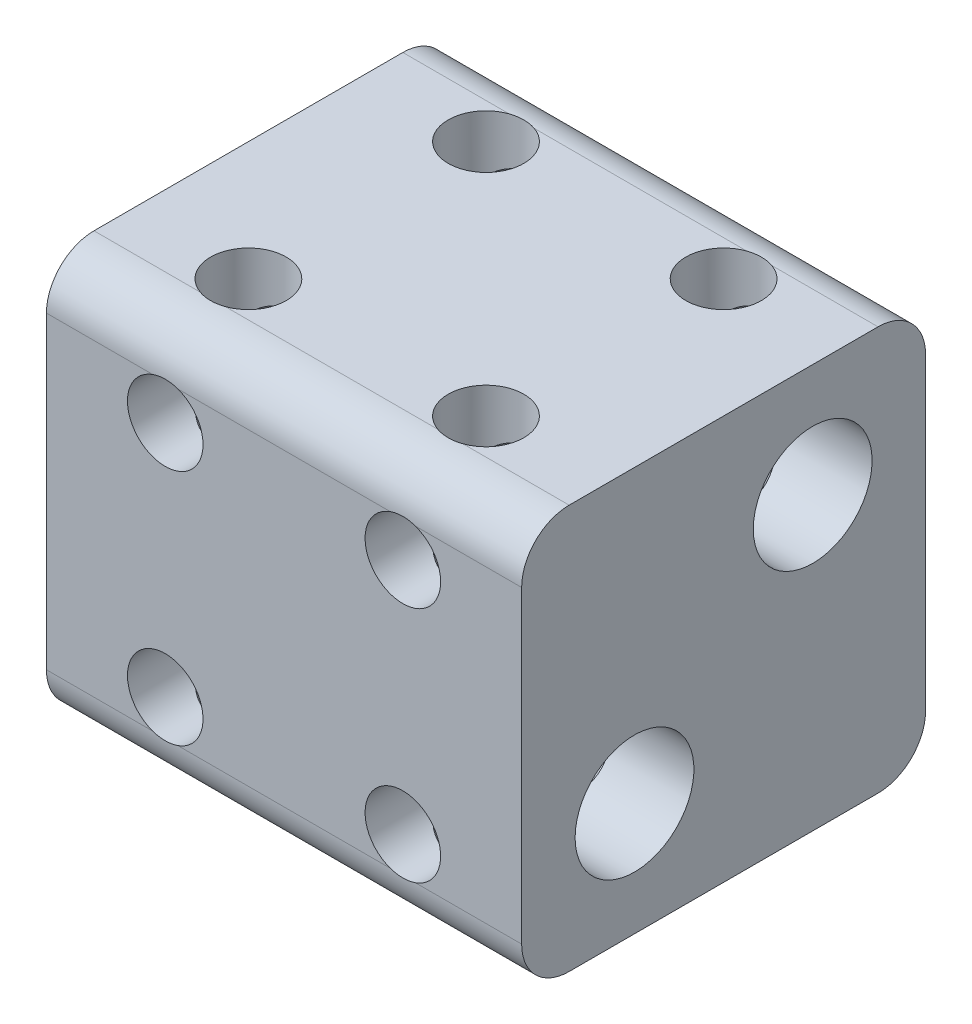
SolidWorks part; units mm, degrees
material "PET"
ref_plane "Front" through (0, 0, 0) normal (0, 0, 1) x (1, 0, 0)
ref_plane "Top" through (0, 0, 0) normal (0, 1, 0) x (1, 0, 0)
ref_plane "Right" through (0, 0, 0) normal (1, 0, 0) x (0, 0, -1)
sketch "Sketch1" plane through (0, 0, 0) normal (1, 0, 0) x (0, 0, -1)
  line L1 (8.255, -10.795) -> (-8.255, -10.795)
  line L2 (10.795, -8.255) -> (10.795, 8.255)
  line L3 (8.255, 10.795) -> (-8.255, 10.795)
  line L4 (-10.795, -8.255) -> (-10.795, 8.255)
  line L5 (10.795, -10.795) -> (-10.795, 10.795) construction
  line L6 (10.795, 10.795) -> (-10.795, -10.795) construction
  arc A0 (10.795, 8.255) -> (8.255, 10.795) centre (8.255, 8.255) ccw
  arc A1 (8.255, -10.795) -> (10.795, -8.255) centre (8.255, -8.255) ccw
  arc A2 (-8.255, -10.795) -> (-10.795, -8.255) centre (-8.255, -8.255) cw
  arc A3 (-8.255, 10.795) -> (-10.795, 8.255) centre (-8.255, 8.255) ccw
  point P0 (0, 0)
  dimension "D2" = 2.54
  dimension "D1" = 21.59
extrude "Boss-Extrude1" add sketch "Sketch1" along normal blind 25.4
sketch "Sketch4" plane through (0, 0, 0) normal (-1, 0, 0) x (0, 0, 1)
  line L0 (-4.7625, 4.7625) -> (4.7625, -4.7625) construction
  point P0 (-4.7625, 4.7625)
  point P2 (4.7625, -4.7625)
  dimension "D1" = 9.525
  dimension "D2" = 9.525
hole_wizard "1/4 (0.2500) Dowel Hole1" positions "Sketch4" profile "Sketch3" hole size "1/4" standard "ANSI Inch" end condition through all
sketch "Sketch3" plane through (0, 4.7625, -4.7625) normal (0, 1, 0) x (0, 0, 1)
  line L0 (0, 0) -> (0, 25.4)
  line L1 (0, 25.4) -> (3.175, 25.4)
  line L2 (3.175, 25.4) -> (3.175, 0)
  line L5 (3.175, 0) -> (0, 0)
  line L11 (0, -6.35) -> (0, 107.95) construction
  dimension "Thru Hole Dia." = 6.35
  dimension "Thru Hole Depth" = 25.4
sketch "Sketch7" plane through (0, 0, 10.795) normal (0, 0, 1) x (1, 0, 0)
  line L0 (0, -10.795) -> (6.35, -6.35) construction
  line L3 (0, 10.795) -> (6.35, 6.35) construction
  line L4 (0, 10.795) -> (0, 8.255) construction
  point P0 (6.35, 6.35)
  point P2 (19.05, 6.35)
  point P5 (6.35, -6.35)
  point P7 (19.05, -6.35)
  dimension "D1" = 12.7
  dimension "D2" = 12.7
  dimension "D3" = 6.35
hole_wizard "#10-32 Tapped Hole2" positions "Sketch7" profile "Sketch6" tap size "#10-32" standard "ANSI Inch" end condition through all
sketch "Sketch6" plane through (6.35, 6.35, 10.795) normal (1, 0, 0) x (0, -1, 0)
  line L0 (0, 0) -> (0, 21.59)
  line L1 (0, 21.59) -> (2.0193, 21.59)
  line L2 (2.0193, 21.59) -> (2.0193, 0)
  line L5 (2.0193, 0) -> (0, 0)
  line L11 (0, -6.35) -> (0, 107.95) construction
  dimension "Thru Tap Drill Dia." = 4.0386
  dimension "Thru Tap Drill Depth" = 21.59
cosmetic thread "Hole Thread3"
cosmetic thread "Hole Thread4"
cosmetic thread "Hole Thread5"
cosmetic thread "Hole Thread6"
ref_plane "Plane1" through (0, 0, 0) normal (0, -0.7071, 0.7071) x (1, 0, 0)
mirror "Mirror1" about plane through (0, 0, 0) normal (0, -0.7071, 0.7071) of "#10-32 Tapped Hole2"
cosmetic thread "Hole Thread7"
cosmetic thread "Hole Thread8"
cosmetic thread "Hole Thread9"
cosmetic thread "Hole Thread10"
